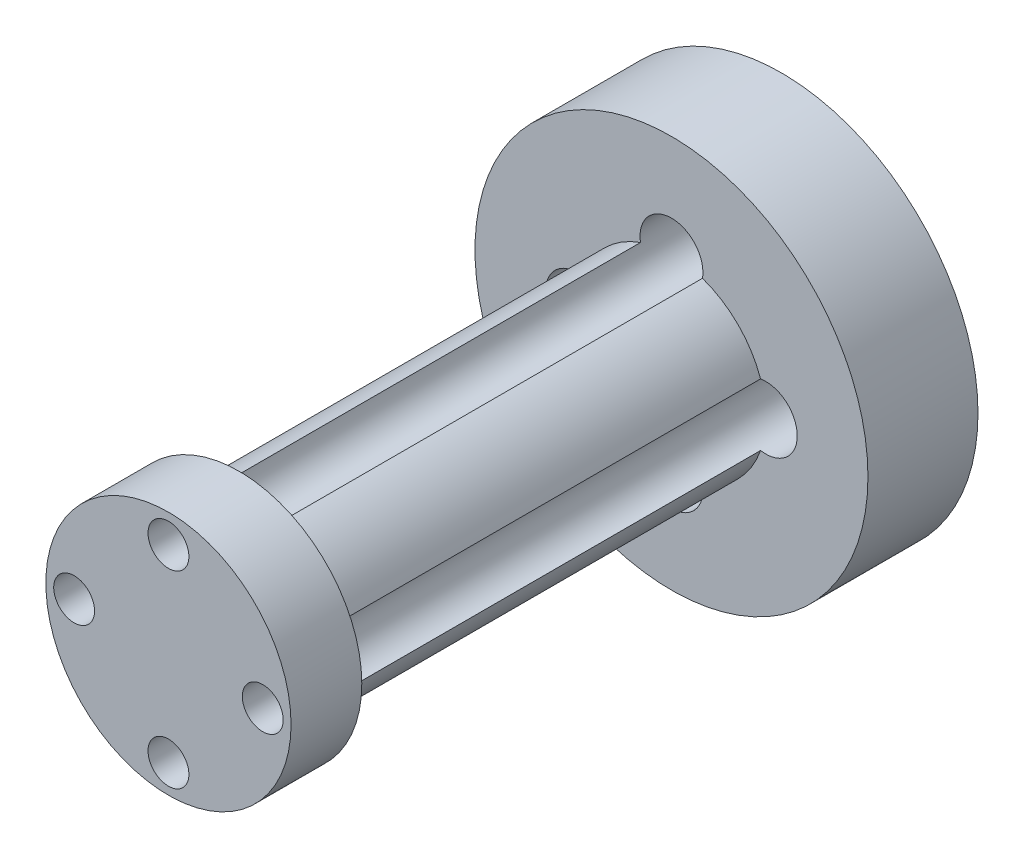
SolidWorks part; units mm, degrees
ref_plane "Front Plane" through (0, 0, 0) normal (0, 0, 1) x (1, 0, 0)
ref_plane "Top Plane" through (0, 0, 0) normal (0, 1, 0) x (1, 0, 0)
ref_plane "Right Plane" through (0, 0, 0) normal (1, 0, 0) x (0, 0, -1)
sketch "Sketch1" plane through (0, 0, 0) normal (0, 0, 1) x (1, 0, 0)
  circle A0 centre (0, 0) radius 12.5
  dimension "D1" = 25
extrude "Boss-Extrude1" add sketch "Sketch1" along normal blind 7
sketch "Sketch2" plane through (0, 0, 7) normal (0, 0, 1) x (1, 0, 0)
  circle A0 centre (0, 0) radius 6
  dimension "D1" = 12
extrude "Boss-Extrude2" add sketch "Sketch2" along normal blind 27.5
sketch "Sketch3" plane through (0, 0, 34.5) normal (0, 0, 1) x (1, 0, 0)
  circle A0 centre (0, 6) radius 2
  circle A1 centre (0, 0) radius 6 construction
  circle A2 centre (6, 0) radius 2
  circle A3 centre (0, -6) radius 2
  circle A4 centre (-6, 0) radius 2
  point P13 (0, 0)
  dimension "D1" = 4
  dimension "D2" = 4
extrude "Cut-Extrude1" cut sketch "Sketch3" against normal through all
sketch "Sketch4" plane through (0, 0, 0) normal (0, 0, -1) x (-1, 0, 0)
  line L0 (0, 0) -> (5.7276, 5.7276)
  circle A1 centre (5.7276, 5.7276) radius 2.07
  circle A2 centre (-5.7276, -5.7276) radius 2.07
  point P9 (0, 0)
  dimension "D2" = 4.14
  dimension "D1" = 8.1
  dimension "D3" = 2
extrude "Cut-Extrude2" cut sketch "Sketch4" against normal blind 5 contours A2 | A1
sketch "Sketch5" plane through (0, 0, 34.5) normal (0, 0, 1) x (1, 0, 0)
  circle A0 centre (0, 0) radius 7.8
  dimension "D1" = 15.6
extrude "Boss-Extrude3" add sketch "Sketch5" along normal blind 4.5
sketch "Sketch6" plane through (0, 0, 39) normal (0, 0, 1) x (1, 0, 0)
  circle A0 centre (-6, 0) radius 1.3
  circle A1 centre (0, 6) radius 1.3
  circle A2 centre (6, 0) radius 1.3
  circle A3 centre (0, -6) radius 1.3
  point P12 (0, 0)
  dimension "D1" = 6
  dimension "D2" = 2.6
  dimension "D3" = 4
extrude "Cut-Extrude3" cut sketch "Sketch6" against normal blind 4.5
